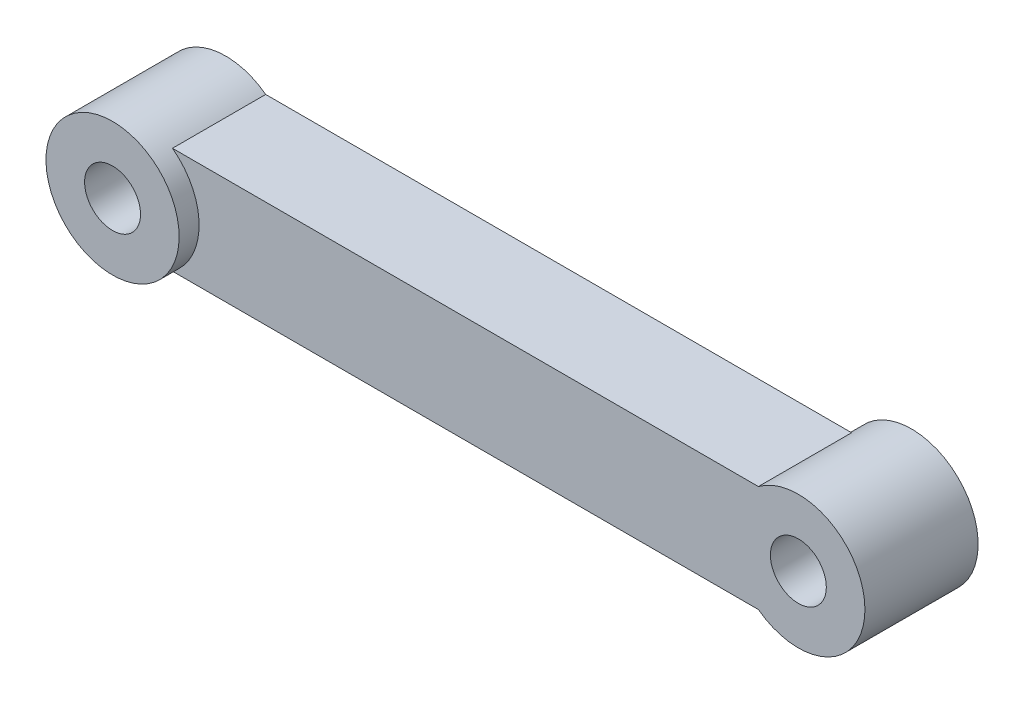
SolidWorks part; units mm, degrees
ref_plane "Front Plane" through (0, 0, 0) normal (0, 0, 1) x (1, 0, 0)
ref_plane "Top Plane" through (0, 0, 0) normal (0, 1, 0) x (1, 0, 0)
ref_plane "Right Plane" through (0, 0, 0) normal (1, 0, 0) x (0, 0, -1)
sketch "Sketch2" plane through (0, 0, 0) normal (0, 0, 1) x (1, 0, 0)
  line L0 (-40.0217, -5.7639) -> (-40.0217, 2.2361)
  line L1 (3.9783, -5.7639) -> (3.9783, 2.2361)
  line L2 (-40.0217, 2.2361) -> (3.9783, 2.2361)
  line L3 (-40.0217, -5.7639) -> (3.9783, -5.7639)
  circle A0 centre (-43.0217, -1.7639) radius 5
  circle A1 centre (6.9783, -1.7639) radius 5
  circle A2 centre (6.9783, -1.7639) radius 2.1
  circle A3 centre (-43.0217, -1.7639) radius 2.1
  dimension "D1" = 10
  dimension "D2" = 10
  dimension "D5" = 4.2
  dimension "D6" = 4.2
  dimension "D3" = 3
  dimension "D4" = 3
  dimension "D7" = 50
extrude "Boss-Extrude1" add sketch "Sketch2" along normal blind 7 contours L0 A0 A3 | L0 A0 | A1 L2 A0 L3 | L1 A1 A2 | L1 A1
sketch "Sketch3" plane through (0, 0, 7) normal (0, 0, 1) x (1, 0, 0)
  circle A0 centre (-43.0217, -1.7639) radius 2.1
  circle A1 centre (-43.0217, -1.7639) radius 5
  dimension "D1" = 10
  dimension "D2" = 4.2
extrude "Boss-Extrude2" add sketch "Sketch3" along normal blind 1.5
sketch "Sketch4" plane through (0, 0, 0) normal (0, 0, -1) x (-1, 0, 0)
  circle A0 centre (-6.9783, -1.7639) radius 2.1
  circle A1 centre (-6.9783, -1.7639) radius 5
  dimension "D1" = 4.2
  dimension "D2" = 10
extrude "Boss-Extrude3" add sketch "Sketch4" along normal blind 1.5
